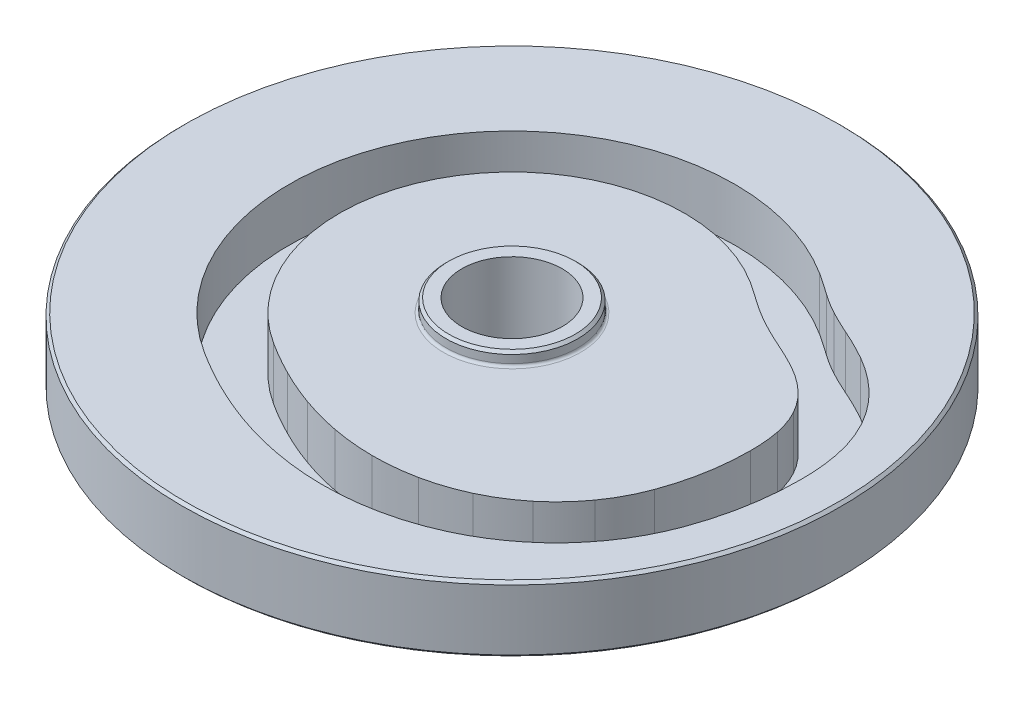
SolidWorks part; units mm, degrees
ref_plane "Front" through (0, 0, 0) normal (0, 0, 1) x (1, 0, 0)
ref_plane "Top" through (0, 0, 0) normal (0, 1, 0) x (1, 0, 0)
ref_plane "Right" through (0, 0, 0) normal (1, 0, 0) x (0, 0, -1)
sketch "Sketch1" plane through (0, 0, 0) normal (0, 0, 1) x (1, 0, 0)
  line L0 (0, -30350) -> (0, 355) construction
  line L1 (19.05, 5) -> (24, 5)
  line L2 (24, 5) -> (25, 4)
  line L3 (25, 4) -> (25, 1)
  line L4 (26, 0) -> (124, 0)
  line L5 (124, 0) -> (125, -1)
  line L6 (125, -1) -> (125, -24)
  line L7 (125, -24) -> (124, -25)
  line L8 (124, -25) -> (26, -25)
  line L9 (25, -26) -> (25, -29)
  line L10 (25, -29) -> (24, -30)
  line L11 (24, -30) -> (19.05, -30)
  line L12 (19.05, -30) -> (19.05, 5)
  arc A0 (25, 1) -> (26, 0) centre (26, 1) ccw
  arc A1 (26, -25) -> (25, -26) centre (26, -26) ccw
revolve "Base-Revolve" add sketch "Sketch1" angle 360 about L0
sketch "Sketch2" plane through (0, 0, 0) normal (0, 1, 0) x (1, 0, 0)
  line L0 (0, 0) -> (100, 0) construction
  arc A0 (100, 0) -> (98.8357, 13.0115) centre (35.1621, 0.756) ccw
  arc A1 (98.8357, 13.0115) -> (94.4055, 25.2692) centre (56.5582, 4.6609) ccw
  arc A2 (94.4055, 25.2692) -> (86.4082, 35.5582) centre (57.7012, 4.9924) ccw
  arc A3 (86.4082, 35.5582) -> (76.1666, 43.0686) centre (49.5088, -4.0212) ccw
  arc A4 (76.1666, 43.0686) -> (65.7386, 48.2775) centre (17.0985, -62.1401) ccw
  arc A5 (65.7386, 48.2775) -> (56.4654, 52.7493) centre (126.41, 185.9441) cw
  arc A6 (56.4654, 52.7493) -> (48.2764, 57.8032) centre (97.8381, 128.9475) cw
  arc A7 (48.2764, 57.8032) -> (40.2312, 63.2965) centre (-118.4006, -177.6649) ccw
  arc A8 (40.2312, 63.2965) -> (-40.2312, -63.2965) centre (0, 0) ccw
  arc A9 (-40.2312, -63.2965) -> (-27.3421, -70.6474) centre (40.8941, 63.9741) ccw
  arc A10 (-27.3421, -70.6474) -> (-12.9935, -76.8335) centre (29.3243, 41.0558) ccw
  arc A11 (-12.9935, -76.8335) -> (2.9489, -81.1965) centre (23.1016, 23.7507) ccw
  arc A12 (2.9489, -81.1965) -> (20.2342, -82.8956) centre (20.8417, 12.0552) ccw
  arc A13 (20.2342, -82.8956) -> (38.1992, -81.1273) centre (20.7804, 3.6953) ccw
  arc A14 (38.1992, -81.1273) -> (55.8267, -75.3156) centre (22.0381, -2.4696) ccw
  arc A15 (55.8267, -75.3156) -> (71.86, -65.2672) centre (23.9693, -6.6684) ccw
  arc A16 (71.86, -65.2672) -> (84.9698, -51.2829) centre (25.8253, -8.9741) ccw
  arc A17 (84.9698, -51.2829) -> (93.9693, -34.202) centre (26.92, -9.7867) ccw
  arc A18 (93.9693, -34.202) -> (100, 0) centre (0, 0) ccw
extrude "Cut-Extrude-Thin1" cut sketch "Sketch2" along normal blind 15 and the other way blind 20 thin
